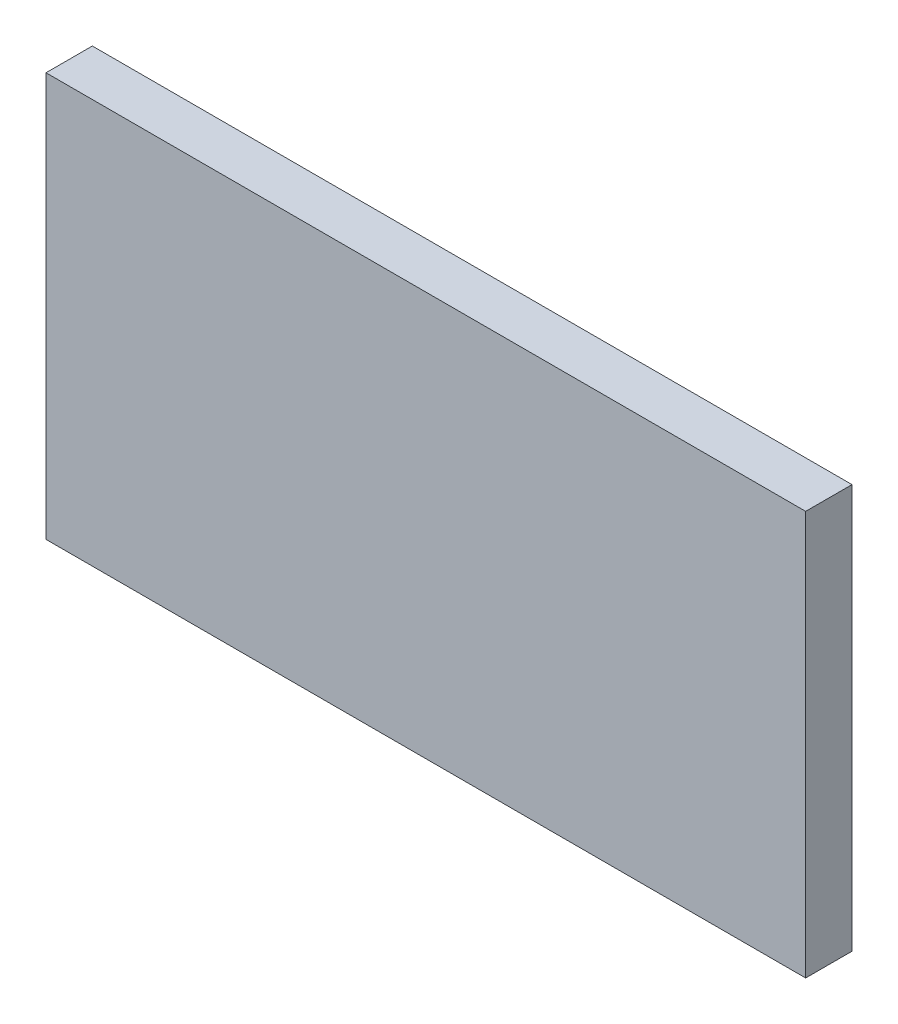
SolidWorks part; units mm, degrees
ref_plane "Plan de face" through (0, 0, 0) normal (0, 0, 1) x (1, 0, 0)
ref_plane "Plan de dessus" through (0, 0, 0) normal (0, 1, 0) x (1, 0, 0)
ref_plane "Plan de droite" through (0, 0, 0) normal (1, 0, 0) x (0, 0, -1)
sketch "Esquisse1" plane through (0, 0, 0) normal (0, 0, 1) x (1, 0, 0)
  line L0 (-125.25, 840.371) -> (125.25, 840.371) construction
  line L1 (-125, 842.371) -> (125, 842.371)
  line L2 (-125, 842.371) -> (-125, 975.371)
  line L3 (-125, 975.371) -> (125, 975.371)
  line L4 (125, 842.371) -> (125, 975.371)
  line L7 (-115.25, 975.371) -> (-125.25, 975.371) construction
  line L8 (0, 975.371) -> (0, 842.371) construction
  line L9 (0, -8.3875) -> (0, 8.3875) construction
  dimension "D1" = 2
  dimension "D2" = 250
extrude "Boss.-Extru.1" add sketch "Esquisse1" along normal blind 15.25
